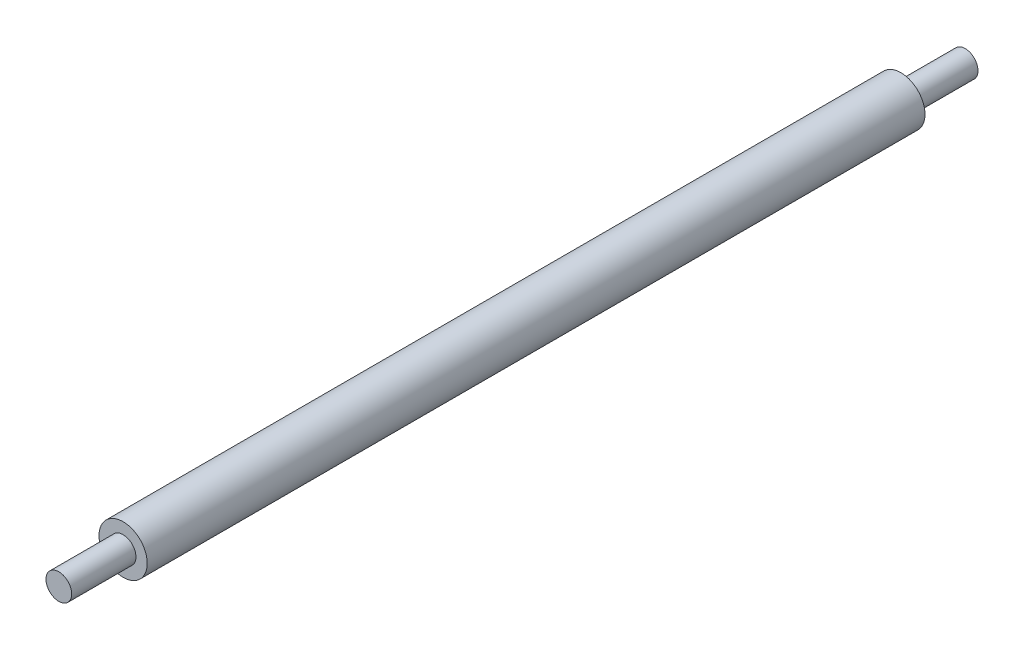
SolidWorks part; units mm, degrees
ref_plane "Front Plane" through (0, 0, 0) normal (0, 0, 1) x (1, 0, 0)
ref_plane "Top Plane" through (0, 0, 0) normal (0, 1, 0) x (1, 0, 0)
ref_plane "Right Plane" through (0, 0, 0) normal (1, 0, 0) x (0, 0, -1)
sketch "Sketch1" plane through (0, 0, 0) normal (0, 0, 1) x (1, 0, 0)
  circle A0 centre (0, 0) radius 7.5
  dimension "D1" = 15
extrude "Boss-Extrude1" add sketch "Sketch1" along normal blind 242
sketch "Sketch2" plane through (0, 0, 242) normal (0, 0, 1) x (1, 0, 0)
  circle A0 centre (0, 0) radius 4
  dimension "D1" = 8
extrude "Boss-Extrude2" add sketch "Sketch2" along normal blind 20
ref_plane "Plane1" through (0, 0, 121) normal (0, 0, 1) x (1, 0, 0)
mirror "Mirror1" about plane through (0, 0, 121) normal (0, 0, 1) of "Boss-Extrude2"
